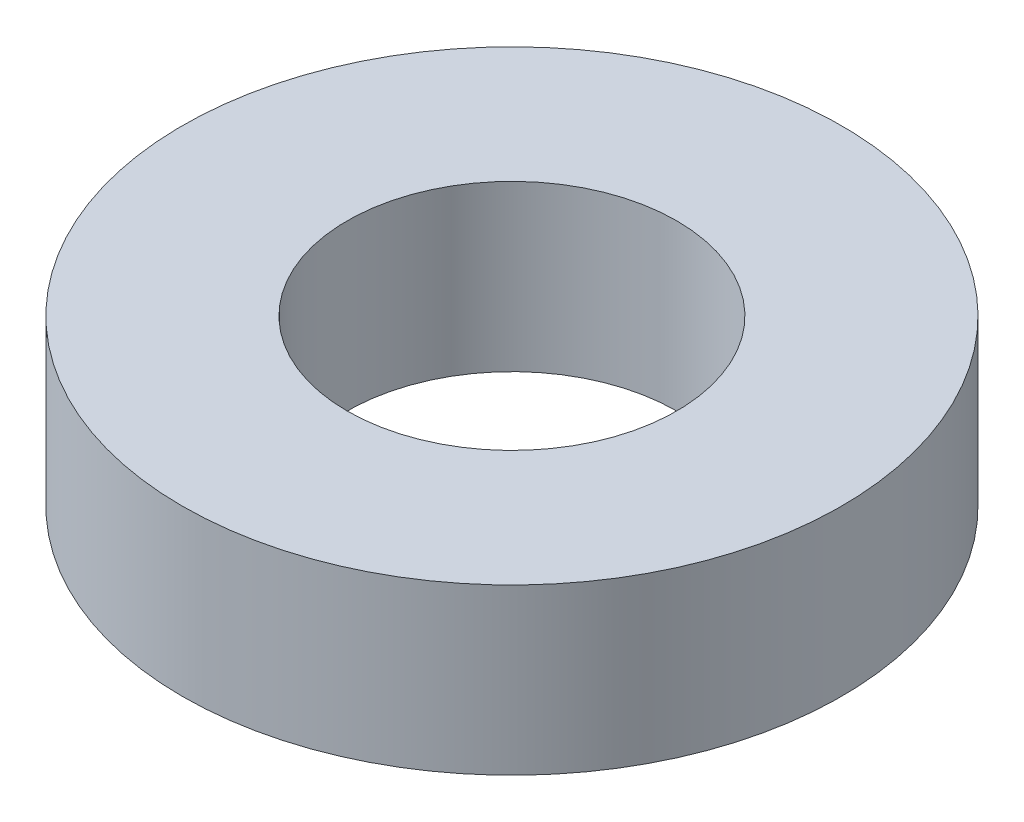
SolidWorks part; units mm, degrees
ref_plane "前视基准面" through (0, 0, 0) normal (0, 0, 1) x (1, 0, 0)
ref_plane "上视基准面" through (0, 0, 0) normal (0, 1, 0) x (1, 0, 0)
ref_plane "右视基准面" through (0, 0, 0) normal (1, 0, 0) x (0, 0, -1)
sketch "草图1" plane through (0, 0, 0) normal (0, 1, 0) x (1, 0, 0)
  circle A0 centre (0, 0) radius 40
  circle A1 centre (0, 0) radius 20
  dimension "D1" = 80
  dimension "D2" = 40
extrude "凸台-拉伸1" add sketch "草图1" along normal blind 20
